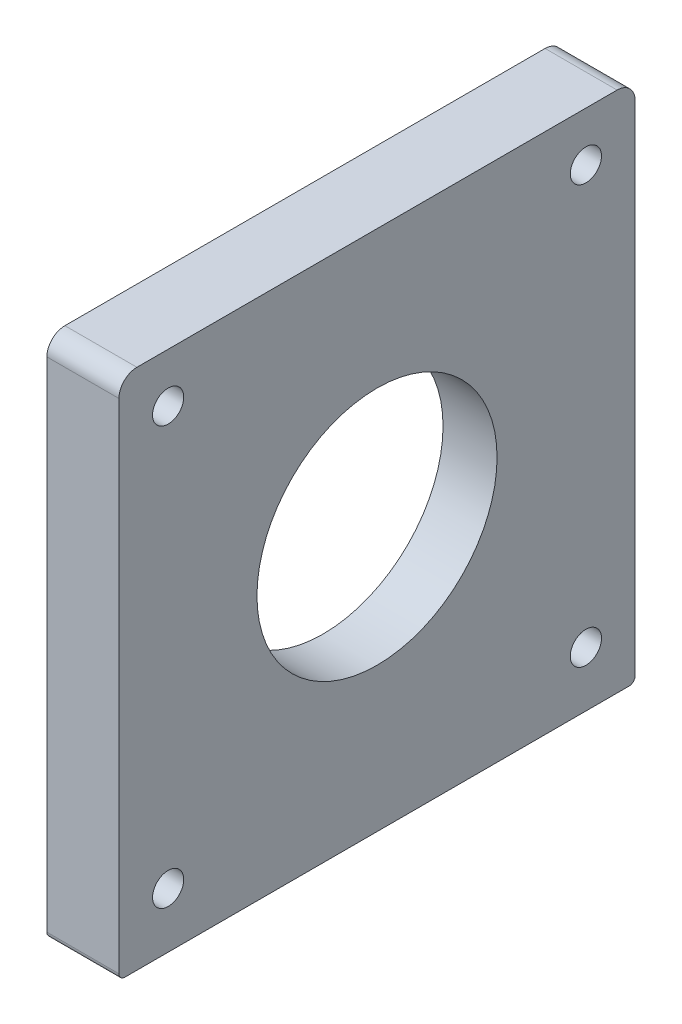
SolidWorks part; units mm, degrees
ref_plane "Front Plane" through (0, 0, 0) normal (0, 0, 1) x (1, 0, 0)
ref_plane "Top Plane" through (0, 0, 0) normal (0, 1, 0) x (1, 0, 0)
ref_plane "Right Plane" through (0, 0, 0) normal (1, 0, 0) x (0, 0, -1)
sketch "Sketch1" plane through (0, 0, 0) normal (0, 1, 0) x (1, 0, 0)
  line L1 (0, 0) -> (40, 0)
  line L2 (0, 0) -> (0, -86)
  line L3 (0, -86) -> (40, -86)
  line L4 (40, 0) -> (40, -86)
  dimension "D1" = 40
  dimension "D2" = 86
extrude "Boss-Extrude1" add sketch "Sketch1" along normal blind 12
sketch "Sketch2" plane through (0, 12, 0) normal (0, 1, 0) x (1, 0, 0)
  line L0 (0, -86) -> (40, -86) construction
  line L1 (40, 0) -> (28, 0)
  line L2 (40, 0) -> (40, -86)
  line L3 (40, -86) -> (28, -86)
  line L4 (28, 0) -> (28, -86)
  dimension "D1" = 12
extrude "Boss-Extrude2" add sketch "Sketch2" along normal blind 87
sketch "Sketch3" plane through (0, 12, 0) normal (0, 1, 0) x (1, 0, 0)
  line L0 (0, -43) -> (62.3366, -43) construction
  line L1 (0, 0) -> (0, -86) construction
  circle A0 centre (14, -8.4) radius 3
  circle A1 centre (14, -77.6) radius 3
  dimension "D1" = 34.6
  dimension "D2" = 6
  dimension "D3" = 14
extrude "Cut-Extrude1" cut sketch "Sketch3" against normal through all
sketch "Sketch4" plane through (28, 0, 0) normal (-1, 0, 0) x (0, 0, 1)
  circle A0 centre (43, 56) radius 38
  dimension "D1" = 76
extrude "Cut-Extrude2" cut sketch "Sketch4" against normal blind 3
sketch "Sketch5" plane through (28, 0, 0) normal (-1, 0, 0) x (0, 0, 1)
  circle A0 centre (77.8, 90.8) radius 2.6
  circle A1 centre (77.8, 21.2) radius 2.6
  circle A2 centre (8.2, 90.8) radius 2.6
  circle A3 centre (8.2, 21.2) radius 2.6
  dimension "D1" = 5.2
extrude "Cut-Extrude3" cut sketch "Sketch5" against normal through all
fillet "Fillet1" radius 3 2 edges at (34, 99, 86) (34, 99, 0)
sketch "Sketch6" plane through (28, 0, 0) normal (-1, 0, 0) x (0, 0, 1)
  circle A0 centre (43, 56) radius 20
  dimension "D1" = 40
extrude "Cut-Extrude4" cut sketch "Sketch6" against normal through all
sketch "Sketch7" plane through (0, 0, 86) normal (0, 0, 1) x (1, 0, 0)
  line L1 (40, 0) -> (0, 0)
  line L2 (40, 0) -> (40, 12)
  line L3 (40, 12) -> (0, 12)
  line L4 (0, 0) -> (0, 12)
extrude "Cut-Extrude5" cut sketch "Sketch7" against normal through all
fillet "Fillet2" radius 1 2 edges at (34, 12, 0) (34, 12, 86)
sketch "Sketch8" plane through (0, 12, 0) normal (0, -1, 0) x (1, 0, 0)
  circle A0 centre (34, 70) radius 2.1
  circle A1 centre (34, 16) radius 2.1
  dimension "D1" = 4.2
extrude "Cut-Extrude6" cut sketch "Sketch8" against normal blind 12
